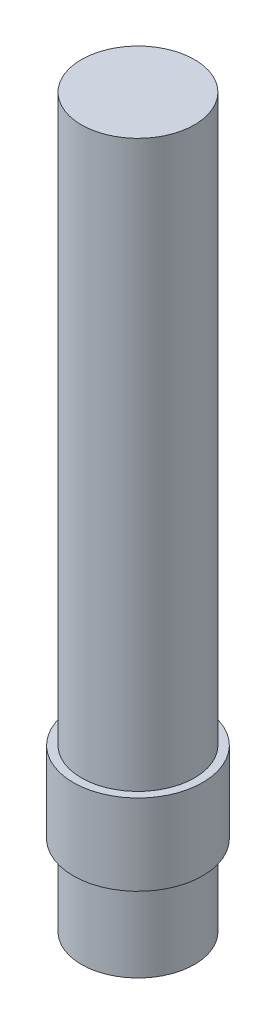
SolidWorks part; units mm, degrees
ref_plane "Front Plane" through (0, 0, 0) normal (0, 0, 1) x (1, 0, 0)
ref_plane "Top Plane" through (0, 0, 0) normal (0, 1, 0) x (1, 0, 0)
ref_plane "Right Plane" through (0, 0, 0) normal (1, 0, 0) x (0, 0, -1)
sketch "Sketch1" plane through (0, 0, 0) normal (0, 1, 0) x (1, 0, 0)
  circle A0 centre (0, 0) radius 3.5
  dimension "D1" = 7
extrude "Boss-Extrude1" add sketch "Sketch1" along normal blind 5
sketch "Sketch2" plane through (0, 5, 0) normal (0, 1, 0) x (1, 0, 0)
  circle A0 centre (0, 0) radius 4
  dimension "D1" = 8
extrude "Boss-Extrude2" add sketch "Sketch2" along normal blind 5
sketch "Sketch3" plane through (0, 10, 0) normal (0, 1, 0) x (1, 0, 0)
  circle A0 centre (0, 0) radius 3.5
  dimension "D1" = 7
extrude "Boss-Extrude3" add sketch "Sketch3" along normal blind 35
